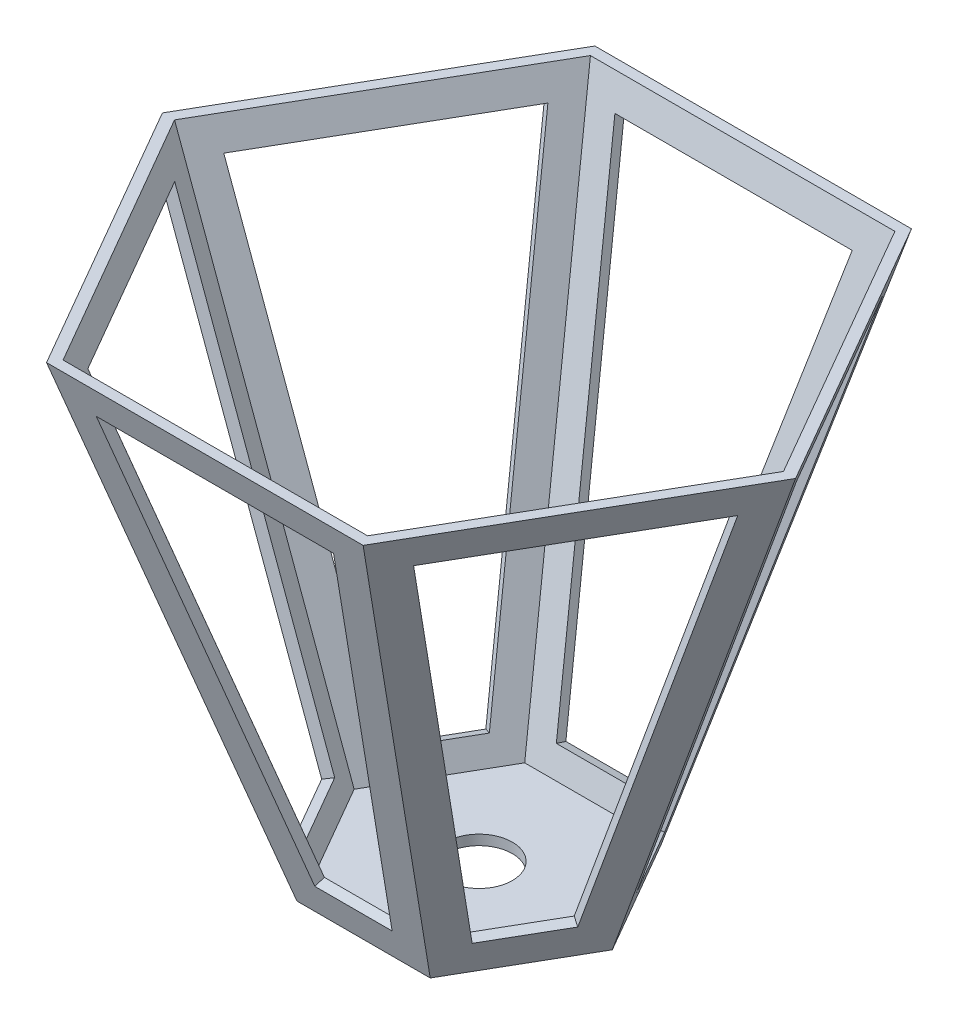
SolidWorks part; units mm, degrees
ref_plane "Front Plane" through (0, 0, 0) normal (0, 0, 1) x (1, 0, 0)
ref_plane "Top Plane" through (0, 0, 0) normal (0, 1, 0) x (1, 0, 0)
ref_plane "Right Plane" through (0, 0, 0) normal (1, 0, 0) x (0, 0, -1)
sketch "Croquis1" plane through (0, 0, 0) normal (0, 1, 0) x (1, 0, 0)
  line L1 (-40, 0) -> (-20, -34.641)
  line L2 (-20, -34.641) -> (20, -34.641)
  line L3 (20, -34.641) -> (40, 0)
  line L4 (40, 0) -> (20, 34.641)
  line L5 (20, 34.641) -> (-20, 34.641)
  line L6 (-20, 34.641) -> (-40, 0)
  circle A0 centre (0, 0) radius 40 construction
  dimension "D1" = 80
ref_plane "Plano1" through (0, 150, 0) normal (0, 1, 0) x (-1, 0, 0)
sketch "Croquis2" plane through (0, 150, 0) normal (0, 1, 0) x (-1, 0, 0)
  line L1 (-95, 0) -> (-47.5, -82.2724)
  line L2 (-47.5, -82.2724) -> (47.5, -82.2724)
  line L3 (47.5, -82.2724) -> (95, 0)
  line L4 (95, 0) -> (47.5, 82.2724)
  line L5 (47.5, 82.2724) -> (-47.5, 82.2724)
  line L6 (-47.5, 82.2724) -> (-95, 0)
  circle A0 centre (0, 0) radius 95 construction
  dimension "D1" = 190
loft "Recubrir1" add profiles "Croquis2", "Croquis1"
shell "Vaciado1" thickness 3
sketch "Croquis3" plane through (0, -9.9924, 31.468) normal (0, -0.3027, 0.9531) x (1, 0, 0)
  line L14 (-11.5958, 20.4841) -> (11.5958, 20.4841)
  line L15 (11.5958, 20.4841) -> (35.6011, 157.865)
  line L16 (35.6011, 157.865) -> (-35.6011, 157.865)
  line L17 (-35.6011, 157.865) -> (-11.5958, 20.4841)
  line L18 (-11.5958, 20.4841) -> (11.5958, 20.4841)
  line L19 (11.5958, 20.4841) -> (35.6011, 157.865)
  line L20 (35.6011, 157.865) -> (-35.6011, 157.865)
  line L21 (-35.6011, 157.865) -> (-11.5958, 20.4841)
  dimension "D1" = 10
extrude "Cortar-Extruir1" cut sketch "Croquis3" against normal up to next (3 mm away)
sketch "Croquis4" plane through (0, 0, 0) normal (0, -1, 0) x (1, 0, 0)
  circle A0 centre (0, 0) radius 10
  dimension "D1" = 20
extrude "Cortar-Extruir2" cut sketch "Croquis4" against normal up to next
pattern_circular "MatrizC1" count 6 over 360 about axis through (0, 0, 0) along (0, 1, 0) of "Cortar-Extruir1"
